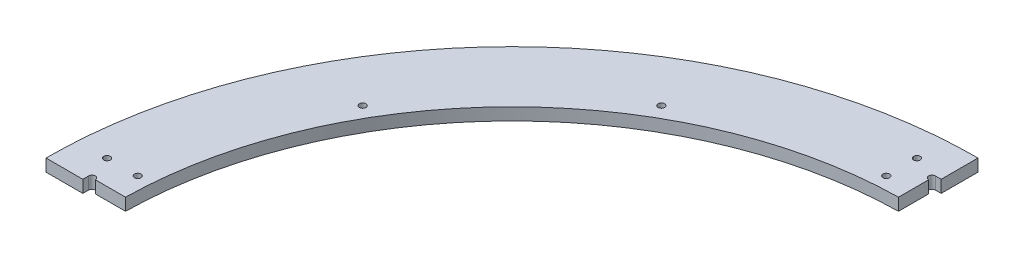
SolidWorks part; units mm, degrees
material "PE High Density"
ref_plane "Front Plane" through (0, 0, 0) normal (0, 0, 1) x (1, 0, 0)
ref_plane "Top Plane" through (0, 0, 0) normal (0, 1, 0) x (1, 0, 0)
ref_plane "Right Plane" through (0, 0, 0) normal (1, 0, 0) x (0, 0, -1)
sketch "Sketch1" plane through (0, 0, 0) normal (0, 1, 0) x (1, 0, 0)
  line L0 (-406.4, 0) -> (-482.6, 0)
  line L1 (406.4, 0) -> (482.6, 0)
  arc A0 (-406.4, 0) -> (406.4, 0) centre (0, 0) cw
  arc A1 (-482.6, 0) -> (482.6, 0) centre (0, 0) cw
  dimension "D2" = 406.4
  dimension "D1" = 76.2
extrude "Boss-Extrude1" add sketch "Sketch1" along normal blind 12.7
sketch "Sketch2" plane through (0, 12.7, 0) normal (0, 1, 0) x (1, 0, 0)
  line L1 (-6.35, 406.3504) -> (6.35, 406.3504)
  line L2 (-6.35, 406.3504) -> (-6.35, 444.5)
  line L3 (-6.35, 444.5) -> (6.35, 444.5)
  line L4 (6.35, 406.3504) -> (6.35, 444.5)
  line L8 (406.3504, 6.35) -> (444.5, 6.35)
  line L9 (0, 0) -> (0, 406.3504) construction
  line L14 (0, 482.6) -> (0, 406.4) construction
  line L15 (406.3504, 6.35) -> (406.3504, -6.35)
  line L16 (406.3504, -6.35) -> (444.5, -6.35)
  line L17 (444.5, 6.35) -> (444.5, -6.35)
  line L18 (6.35, -406.3504) -> (6.35, -444.5)
  line L19 (6.35, -406.3504) -> (-6.35, -406.3504)
  line L20 (-6.35, -406.3504) -> (-6.35, -444.5)
  line L21 (6.35, -444.5) -> (-6.35, -444.5)
  line L22 (-406.3504, -6.35) -> (-444.5, -6.35)
  line L23 (-406.3504, -6.35) -> (-406.3504, 6.35)
  line L24 (-406.3504, 6.35) -> (-444.5, 6.35)
  line L25 (-444.5, -6.35) -> (-444.5, 6.35)
  arc A0 (406.4, 0) -> (-406.4, 0) centre (0, 0) ccw construction
  arc A1 (482.6, 0) -> (-482.6, 0) centre (0, 0) ccw construction
  point P7 (0, 406.3504)
  point P16 (0, 0)
  point P23 (0, 444.5)
  point P33 (0, 0)
  dimension "D1" = 38.1
  dimension "D2" = 12.7
  dimension "D3" = 4
extrude "Cut-Extrude1" cut sketch "Sketch2" against normal through all
sketch "Sketch3" plane through (0, 12.7, 0) normal (0, 1, 0) x (1, 0, 0)
  line L0 (-6.35, 444.5) -> (-6.35, 441.071) construction
  line L1 (6.35, 444.5) -> (-6.35, 444.5) construction
  line L2 (0, 444.5) -> (0, 0) construction
  line L3 (-444.5, 6.35) -> (-441.071, 6.35) construction
  line L5 (-6.35, 444.5) -> (-6.35, 406.3504) construction
  line L6 (-406.3504, 6.35) -> (-444.5, 6.35) construction
  circle A0 centre (-6.35, 441.071) radius 3.429
  circle A1 centre (-441.071, 6.35) radius 3.429
  circle A2 centre (6.35, 441.071) radius 3.429
  circle A3 centre (441.071, 6.35) radius 3.429
  dimension "D1" = 6.858
extrude "Cut-Extrude2" cut sketch "Sketch3" against normal through all contours A1 | A0 | A2 | A3
hole_wizard "1/4 Clearance Hole1" positions "Sketch6" profile "Sketch7" hole size "1/4" standard "ANSI Inch" end condition through all
sketch "Sketch6" plane through (0, 12.7, 0) normal (0, 1, 0) x (1, 0, 0)
  line L0 (0, 444.5) -> (0, 406.4) construction
  line L1 (6.35, 444.5) -> (-6.35, 444.5) construction
  line L2 (0, 406.4) -> (-31.75, 406.4) construction
  line L3 (-31.75, 406.4) -> (-31.75, 419.1) construction
  line L4 (-31.75, 419.1) -> (-31.75, 450.85) construction
  line L6 (-444.5, 0) -> (-406.4, 0) construction
  line L7 (-406.4, 0) -> (-406.4, 31.75) construction
  line L8 (-406.4, 31.75) -> (-419.1, 31.75) construction
  line L9 (-419.1, 31.75) -> (-450.85, 31.75) construction
  line L10 (-6.35, 437.642) -> (-6.35, 406.3504) construction
  line L11 (-406.4, 0) -> (-351.9527, 203.2) construction
  line L12 (-351.9527, 203.2) -> (-203.2, 351.9527) construction
  line L13 (-203.2, 351.9527) -> (0, 406.4) construction
  line L15 (-351.9527, 203.2) -> (-365.7009, 211.1375) construction
  line L16 (-203.2, 351.9527) -> (-211.1375, 365.7009) construction
  line L17 (0, 0) -> (-287.3682, 287.3682) construction
  arc A0 (-6.35, 406.3504) -> (-406.3504, 6.35) centre (0, 0) ccw construction
  point P8 (-31.75, 419.1)
  point P10 (-31.75, 450.85)
  point P21 (-419.1, 31.75)
  point P22 (-450.85, 31.75)
  point P52 (-211.1375, 365.7009)
  point P54 (-365.7009, 211.1375)
  dimension "D1" = 38.1
  dimension "D2" = 25.4
  dimension "D3" = 12.7
  dimension "D4" = 31.75
  dimension "D5" = 15.875
sketch "Sketch7" plane through (-365.7009, 12.7, -211.1375) normal (1, 0, 0) x (0, 0, 1)
  line L0 (0, 0) -> (0, 12.7)
  line L1 (0, 12.7) -> (3.3782, 12.7)
  line L2 (3.3782, 12.7) -> (3.3782, 0)
  line L5 (3.3782, 0) -> (0, 0)
  line L11 (0, -6.35) -> (0, 107.95) construction
  dimension "Thru Hole Dia." = 6.7564
  dimension "Thru Hole Depth" = 12.7
sketch "Sketch8" plane through (0, 12.7, 0) normal (0, 1, 0) x (1, 0, 0)
  line L1 (0, 482.6) -> (482.6, 482.6)
  line L2 (0, 482.6) -> (0, 0)
  line L3 (0, 0) -> (482.6, 0)
  line L4 (482.6, 482.6) -> (482.6, 0)
  arc A0 (482.6, 0) -> (-482.6, 0) centre (0, 0) ccw construction
extrude "Cut-Extrude4" cut sketch "Sketch8" against normal through all
sketch "Sketch9" plane through (0, 12.7, 0) normal (0, 1, 0) x (1, 0, 0)
  line L0 (0, 444.5) -> (-6.35, 444.5) construction
  line L1 (0, 482.6) -> (-0.3175, 482.6)
  line L2 (0, 482.6) -> (0, 444.5)
  line L3 (0, 444.5) -> (-0.3175, 444.5)
  line L4 (-0.3175, 482.6) -> (-0.3175, 444.5)
  line L5 (0, 0) -> (-341.2497, 341.2497) construction
  line L6 (-482.6, 0.3175) -> (-444.5, 0.3175)
  line L7 (-444.5, 0) -> (-444.5, 0.3175)
  line L8 (-482.6, 0) -> (-444.5, 0)
  line L9 (-482.6, 0) -> (-482.6, 0.3175)
  arc A0 (0, 482.6) -> (-482.6, 0) centre (0, 0) ccw construction
  dimension "D1" = 0.3175
extrude "Cut-Extrude5" cut sketch "Sketch9" against normal through all
